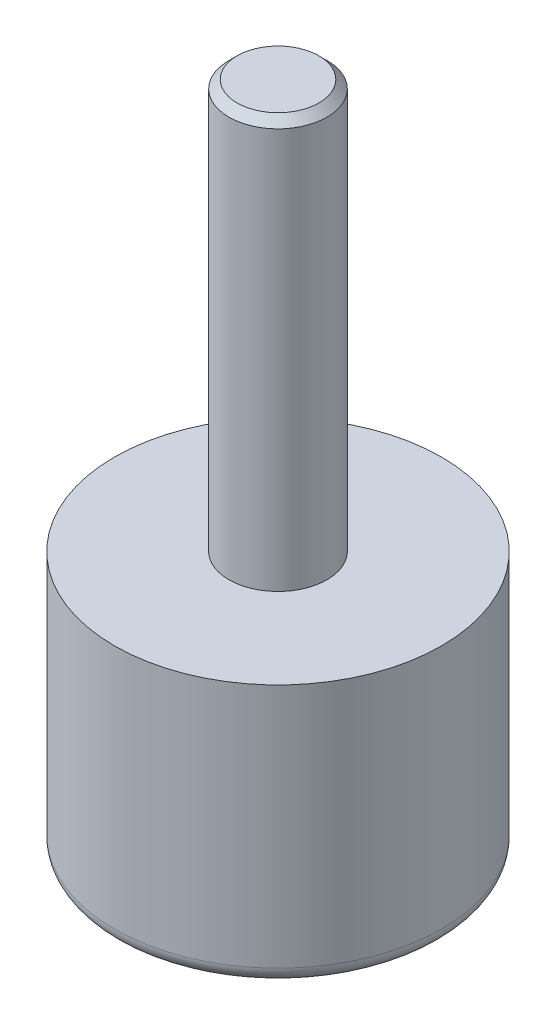
SolidWorks part; units mm, degrees
material "AISI 316 Barre d'acier inoxydable recuit (SS)"
ref_plane "Plan de face" through (0, 0, 0) normal (0, 0, 1) x (1, 0, 0)
ref_plane "Plan de dessus" through (0, 0, 0) normal (0, 1, 0) x (1, 0, 0)
ref_plane "Plan de droite" through (0, 0, 0) normal (1, 0, 0) x (0, 0, -1)
sketch "Esquisse1" plane through (0, 0, 0) normal (0, 0, 1) x (1, 0, 0)
  line L0 (0, 22.5) -> (0, -22.5) construction
  line L1 (-5.831, -18.5) -> (-10, -18.5)
  line L2 (-10, -18.5) -> (-10, -2.5)
  line L3 (-10, -2.5) -> (-3, -2.5)
  line L4 (-3, -2.5) -> (-3, 22.5)
  line L5 (-3, 22.5) -> (0, 22.5)
  line L6 (0, 22.5) -> (0, -22.5)
  arc A0 (0, -22.5) -> (-5.831, -18.5) centre (0, -16.25) cw
  dimension "D5" = 6.25
  dimension "D1" = 20
  dimension "D2" = 20
  dimension "D3" = 45
  dimension "D4" = 6
  dimension "D6" = 16
revolve "Révolution1" add sketch "Esquisse1" angle 360 about L0
cosmetic thread "Représentation de filetage1" parameters "D2"=5
chamfer "Chanfrein1" distance 0.5 angle 45 1 edges at (0, 22.5, 3)
fillet "Congé1" radius 1 1 edges at (0, -18.5, 10)
